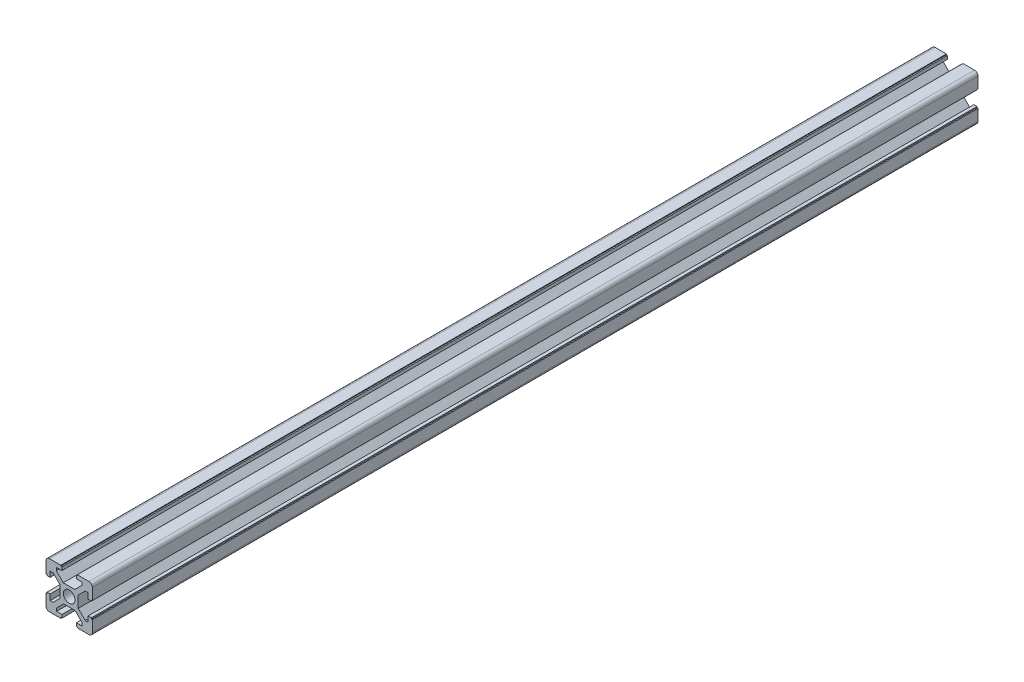
SolidWorks part; units mm, degrees
ref_plane "Front Plane" through (0, 0, 0) normal (0, 0, 1) x (1, 0, 0)
ref_plane "Top Plane" through (0, 0, 0) normal (0, 1, 0) x (1, 0, 0)
ref_plane "Right Plane" through (0, 0, 0) normal (1, 0, 0) x (0, 0, -1)
sketch "Sketch1" plane through (0, 0, 0) normal (0, 0, 1) x (1, 0, 0)
  line L0 (240.9169, 601.7923) -> (1204.5843, 601.7923) construction
  line L6 (13.0291, 10.3872) -> (13.0291, 12.8554)
  line L7 (12.7291, 6.0212) -> (29.7291, 6.0212)
  line L11 (11.2291, 7.5212) -> (11.2291, 24.3895)
  line L12 (12.7291, 25.8895) -> (29.7291, 25.8895)
  line L13 (31.2291, 7.5212) -> (31.2291, 24.3895)
  line L14 (11.2291, 6.0212) -> (31.2291, 25.8895) construction
  line L15 (11.2291, 25.8895) -> (31.2291, 6.0212) construction
  line L16 (13.0291, 24.0895) -> (13.041, 24.0895)
  line L17 (29.4291, 10.5205) -> (29.4291, 12.8554)
  line L18 (13.0291, 7.8212) -> (13.041, 7.8212)
  line L19 (11.2291, 15.9554) -> (31.2291, 15.9554) construction
  line L20 (11.6567, 12.8554) -> (13.0291, 12.8554)
  line L21 (11.6567, 19.0554) -> (13.0291, 19.0554)
  line L22 (21.2291, 6.0212) -> (21.2291, 25.8895) construction
  line L23 (24.8338, 25.9554) -> (24.8338, 25.5277)
  line L24 (17.3291, 21.0535) -> (17.3291, 19.8297)
  line L25 (11.2291, 19.56) -> (11.6567, 19.56)
  line L26 (11.6567, 19.56) -> (11.6567, 19.0554)
  line L27 (11.6567, 19.0554) -> (13.0291, 19.0554)
  line L28 (17.3291, 18.3778) -> (14.3166, 21.3903)
  line L29 (14.3166, 21.3903) -> (13.0291, 21.3903)
  line L30 (17.3291, 13.3997) -> (14.3166, 10.3872)
  line L31 (14.3166, 10.3872) -> (13.0291, 10.3872)
  line L32 (13.0291, 7.8212) -> (13.0291, 24.0895) construction
  line L33 (29.4172, 7.8212) -> (29.4291, 7.8212)
  line L34 (13.0291, 7.8212) -> (29.4291, 7.8212) construction
  line L35 (17.3291, 12.081) -> (17.3291, 10.641)
  line L36 (24.8338, 25.5277) -> (24.3291, 25.5277)
  line L37 (11.2291, 12.8554) -> (31.2291, 12.8554) construction
  line L38 (24.3291, 25.5277) -> (24.3291, 24.1554)
  line L39 (11.2291, 19.0554) -> (31.2291, 19.0554) construction
  line L40 (17.3291, 18.3778) -> (17.3291, 13.3997)
  line L41 (11.6567, 12.8554) -> (11.6567, 12.3367)
  line L42 (11.6567, 12.3367) -> (11.2291, 12.3367)
  line L43 (13.0291, 19.0554) -> (13.0291, 21.3903)
  line L44 (24.3291, 24.1554) -> (26.664, 24.1554)
  line L45 (26.664, 22.8679) -> (26.664, 24.1554)
  line L46 (23.6515, 19.8554) -> (26.664, 22.8679)
  line L47 (23.6515, 19.8554) -> (18.6734, 19.8554)
  line L48 (18.6734, 19.8554) -> (15.661, 22.8679)
  line L49 (15.661, 24.1554) -> (18.1291, 24.1554)
  line L50 (15.661, 22.8679) -> (15.661, 24.1554)
  line L51 (18.1291, 25.5277) -> (18.1291, 24.1554)
  line L52 (18.1291, 25.5277) -> (17.6104, 25.5277)
  line L53 (17.6104, 25.5277) -> (17.6104, 25.9554)
  line L54 (31.2291, 12.3507) -> (30.8015, 12.3507)
  line L55 (30.8015, 12.3507) -> (30.8015, 12.8554)
  line L56 (30.8015, 12.8554) -> (29.4291, 12.8554)
  line L57 (29.4291, 12.8554) -> (29.4291, 10.5205)
  line L58 (28.1416, 10.5205) -> (29.4291, 10.5205)
  line L59 (25.1291, 13.533) -> (28.1416, 10.5205)
  line L60 (25.1291, 13.533) -> (25.1291, 18.511)
  line L61 (25.1291, 18.511) -> (28.1416, 21.5235)
  line L62 (29.4291, 21.5235) -> (29.4291, 19.0554)
  line L63 (28.1416, 21.5235) -> (29.4291, 21.5235)
  line L64 (30.8015, 19.0554) -> (29.4291, 19.0554)
  line L65 (30.8015, 19.0554) -> (30.8015, 19.5741)
  line L66 (30.8015, 19.5741) -> (31.2291, 19.5741)
  line L67 (17.6244, 5.9554) -> (17.6244, 6.383)
  line L68 (17.6244, 6.383) -> (18.1291, 6.383)
  line L69 (18.1291, 6.383) -> (18.1291, 7.7554)
  line L70 (18.1291, 7.7554) -> (15.7942, 7.7554)
  line L71 (15.7942, 9.0429) -> (15.7942, 7.7554)
  line L72 (18.8067, 12.0554) -> (15.7942, 9.0429)
  line L73 (18.8067, 12.0554) -> (23.7848, 12.0554)
  line L74 (23.7848, 12.0554) -> (26.7973, 9.0429)
  line L75 (26.7973, 7.7554) -> (24.3291, 7.7554)
  line L76 (26.7973, 9.0429) -> (26.7973, 7.7554)
  line L77 (24.3291, 6.383) -> (24.3291, 7.7554)
  line L78 (24.3291, 6.383) -> (24.8478, 6.383)
  line L79 (24.8478, 6.383) -> (24.8478, 5.9554)
  line L80 (29.4172, 24.0895) -> (29.4291, 24.0895)
  line L81 (13.0291, 24.0895) -> (29.4291, 24.0895) construction
  line L82 (29.4291, 19.0554) -> (29.4291, 21.5235)
  line L83 (29.4291, 7.8212) -> (29.4291, 24.0895) construction
  circle A1 centre (21.2291, 15.9554) radius 2.5
  arc A2 (12.7291, 25.8895) -> (11.2291, 24.3895) centre (12.7291, 24.3895) ccw
  arc A3 (11.2291, 7.5212) -> (12.7291, 6.0212) centre (12.7291, 7.5212) ccw
  arc A4 (29.7291, 6.0212) -> (31.2291, 7.5212) centre (29.7291, 7.5212) ccw
  arc A5 (31.2291, 24.3895) -> (29.7291, 25.8895) centre (29.7291, 24.3895) ccw
  arc A6 (13.0291, 24.0895) -> (13.0291, 24.0895) centre (13.0291, 24.0895) ccw
  arc A7 (29.4291, 24.0895) -> (29.4291, 24.0895) centre (29.4291, 24.0895) ccw
  arc A8 (29.4291, 7.8212) -> (29.4291, 7.8212) centre (29.4291, 7.8212) ccw
  arc A9 (13.0291, 7.8212) -> (13.0291, 7.8212) centre (13.0291, 7.8212) ccw
  point P105 (21.2291, 15.9554)
  dimension "D1" = 20
  dimension "D2" = 1.5
  dimension "D3" = 1.5
  dimension "D7" = 4
  dimension "D8" = 6.1
  dimension "D4" = 1.8
  dimension "D5" = 3.1
  dimension "D6" = 3.1
extrude "Boss-Extrude1" add sketch "Sketch1" along normal blind 382
